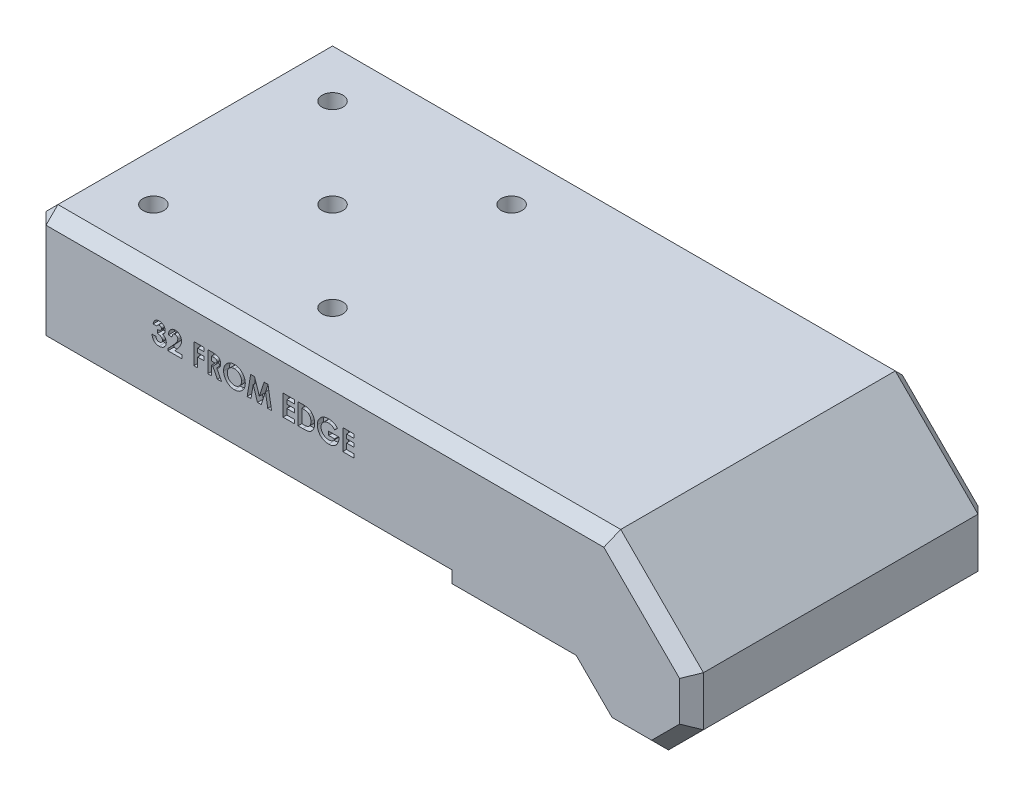
SolidWorks part; units mm, degrees
ref_plane "Front Plane" through (0, 0, 0) normal (0, 0, 1) x (1, 0, 0)
ref_plane "Top Plane" through (0, 0, 0) normal (0, 1, 0) x (1, 0, 0)
ref_plane "Right Plane" through (0, 0, 0) normal (1, 0, 0) x (0, 0, -1)
sketch "Sketch1" plane through (0, 0, 0) normal (0, 0, 1) x (1, 0, 0)
  line L0 (0, 0) -> (0, -14.3) construction
  line L10 (0, -14.3) -> (-154.9378, -14.3) construction
  line L11 (-154.9378, -14.3) -> (-154.9378, 2) construction
  line L12 (-154.9378, 2) -> (-90, 2) construction
  line L17 (6, -6) -> (14.2843, -6)
  line L18 (14.2843, -6) -> (20.1421, -0.1421)
  line L19 (20.1421, -0.1421) -> (20.1421, 8.1421)
  line L20 (20.1421, 8.1421) -> (6.2843, 22)
  line L22 (6.2843, 22) -> (-90, 22)
  line L23 (-90, 22) -> (-90, 2)
  line L24 (-90, 2) -> (-22, 2)
  line L26 (0, 0) -> (6, -6)
  line L30 (-22, 0) -> (-22, 2)
  line L31 (-22, 0) -> (0, 0)
  point P5 (0, 0)
  point P12 (0, 0)
  point P13 (10.1421, -6)
  point P15 (-22, -0.15)
  point P18 (20.1421, 0)
  dimension "D4" = 6
  dimension "D2" = 20
  dimension "D3" = 45
  dimension "D1" = 16.3
  dimension "D5" = 2
  dimension "D6" = 20
  dimension "D7" = 22
  dimension "D12" = 90
extrude "Boss-Extrude1" add sketch "Sketch1" along normal blind 50
sketch "Sketch2" plane through (0, 22, 0) normal (0, 1, 0) x (1, 0, 0)
  line L0 (-90, -25) -> (-44.724, -25) construction
  line L1 (-90, -50) -> (-90, 0) construction
  line L2 (-80, -10) -> (-50, -40) construction
  circle A0 centre (-80, -10) radius 1.75
  circle A1 centre (-50, -10) radius 1.75
  circle A4 centre (-50, -40) radius 1.75
  circle A5 centre (-80, -40) radius 1.75
  circle A6 centre (-65, -25) radius 1.75
  point P10 (-56.6839, -25)
  dimension "D3" = 3.5
  dimension "D2" = 30
  dimension "D4" = 30
  dimension "D5" = 10
  dimension "D1" = 2
extrude "Cut-Extrude1" cut sketch "Sketch2" against normal through all
chamfer "Chamfer1" distance 2 angle 10 5 edges at (-80, 2, 11.75) (-50, 2, 11.75) (-80, 2, 41.75) (-50, 2, 41.75) (-65, 2, 26.75)
sketch "Sketch5" plane through (0, 0, 50) normal (0, 0, 1) x (1, 0, 0)
  text T0 "32 FROM EDGE" font "Century Gothic" height 3.5
extrude "Cut-Extrude2" cut sketch "Sketch5" against normal blind 1
chamfer "Chamfer2" distance 2 angle 45 22 edges at (-90, 22, 25) (-90, 12, 50) (-90, 12, 0) (-41.8579, 22, 0) (13.2132, 15.0711, 0) (20.1421, 4, 0) (17.2132, -3.0711, 0) (10.1421, -6, 0) (3, -3, 0) (-11, 0, 0) (-22, 1, 0) (-56, 2, 0) (-90, 2, 25) (-41.8579, 22, 50) (13.2132, 15.0711, 50) (-56, 2, 50) (-22, 1, 50) (-11, 0, 50) (3, -3, 50) (10.1421, -6, 50) (17.2132, -3.0711, 50) (20.1421, 4, 50)
